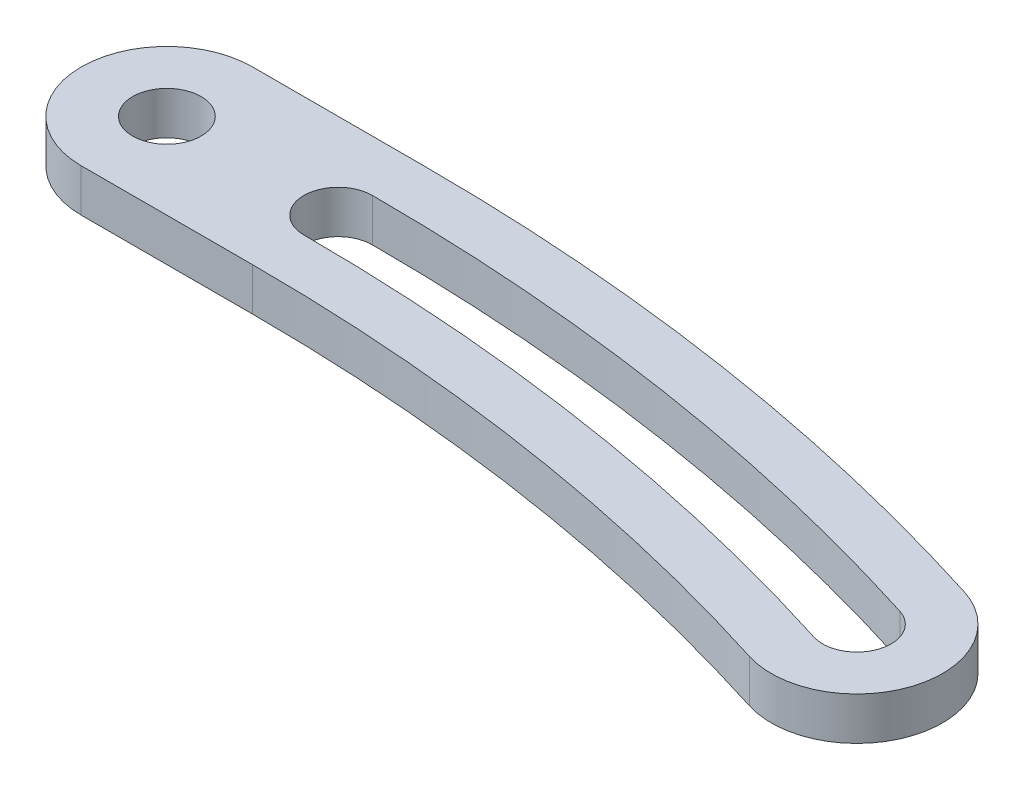
SolidWorks part; units mm, degrees
material "Thornel Mat VMA"
ref_plane "前视基准面" through (0, 0, 0) normal (0, 0, 1) x (1, 0, 0)
ref_plane "上视基准面" through (0, 0, 0) normal (0, 1, 0) x (1, 0, 0)
ref_plane "右视基准面" through (0, 0, 0) normal (1, 0, 0) x (0, 0, -1)
sketch "草图2" plane through (0, 0, 0) normal (0, 1, 0) x (1, 0, 0)
  line L0 (-8, 4) -> (0, 4)
  line L2 (0, 0) -> (-8, 0) construction
  line L5 (-8, -4) -> (0, -4)
  arc A9 (27.4535, -8.2399) -> (29.867, -0.6127) centre (28.6602, -4.4263) ccw
  arc A10 (0, 0) -> (28.6602, -4.4263) centre (0, -95) cw construction
  circle A11 centre (-8, 0) radius 1.6
  arc A12 (-8, 4) -> (-8, -4) centre (-8, 0) ccw
  arc A13 (29.1429, -2.9009) -> (0, 1.6) centre (0, -95) ccw
  arc A14 (28.1775, -5.9518) -> (0, -1.6) centre (0, -95) ccw
  arc A15 (28.1775, -5.9518) -> (29.1429, -2.9009) centre (28.6602, -4.4263) ccw
  arc A16 (0, 1.6) -> (0, -1.6) centre (0, 0) ccw
  arc A17 (0, 4) -> (29.867, -0.6127) centre (0, -95) cw
  arc A18 (27.4535, -8.2399) -> (0, -4) centre (0, -95) ccw
  point P3 (14.5, -1.1131)
  dimension "D2" = 29
  dimension "D3" = 4
  dimension "D4" = 3.2
  dimension "D5" = 8
  dimension "D1" = 95
extrude "凸台-拉伸1" add sketch "草图2" along normal blind 2
